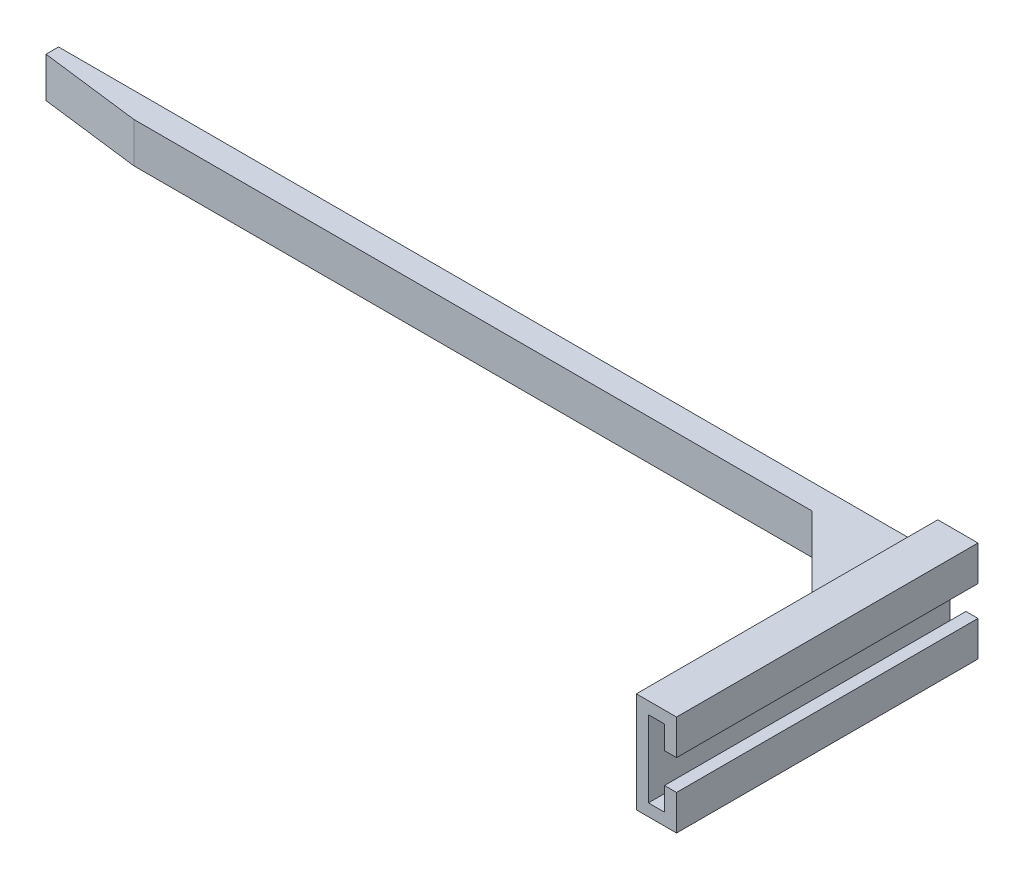
SolidWorks part; units mm, degrees
ref_plane "前视基准面" through (0, 0, 0) normal (0, 0, 1) x (1, 0, 0)
ref_plane "上视基准面" through (0, 0, 0) normal (0, 1, 0) x (1, 0, 0)
ref_plane "右视基准面" through (0, 0, 0) normal (1, 0, 0) x (0, 0, -1)
sketch "草图1" plane through (0, 0, 0) normal (0, 0, 1) x (1, 0, 0)
  line L5 (5.6, 10.6) -> (3.2, 10.6)
  line L6 (0, 0) -> (3.2, 0)
  line L11 (0, 0) -> (0, 15.2)
  line L12 (0, 15.2) -> (3.2, 15.2)
  line L17 (3.2, 0) -> (3.2, 4.6)
  line L18 (-2.4, -2.4) -> (5.6, -2.4)
  line L21 (-2.4, -2.4) -> (-2.4, 17.6)
  line L22 (-2.4, 17.6) -> (5.6, 17.6)
  line L23 (5.6, -2.4) -> (5.6, 4.6)
  line L24 (3.2, 4.6) -> (5.6, 4.6)
  line L25 (3.2, 10.6) -> (3.2, 15.2)
  line L26 (5.6, 10.6) -> (5.6, 17.6)
  point P5 (1.6, 17.6)
  point P9 (1.6, 15.2)
  dimension "D1" = 3.2
  dimension "D2" = 15.2
  dimension "D3" = 8
  dimension "D4" = 20
  dimension "D5" = 0
extrude "凸台-拉伸1" add sketch "草图1" along normal blind 60 contours L12 L25 L5 L26 L22 L21 L18 L23 L24 L17 L6 L11
sketch "草图2" plane through (-2.4, 0, 0) normal (-1, 0, 0) x (0, 0, 1)
  line L0 (0, -2.4) -> (0, 17.6) construction
  line L1 (0, 11.6) -> (5, 11.6)
  line L2 (0, 11.6) -> (0, 3.6)
  line L3 (0, 3.6) -> (5, 3.6)
  line L4 (5, 11.6) -> (5, 3.6)
  line L5 (60, 17.6) -> (0, 17.6) construction
  line L6 (60, -2.4) -> (0, -2.4) construction
  dimension "D1" = 6
  dimension "D2" = 6
  dimension "D3" = 5
extrude "凸台-拉伸2" add sketch "草图2" along normal blind 175 contours L4 L3 L2 L1
chamfer "倒角1" distance 20 angle 45 1 edges at (-2.4, 7.6, 5)
sketch "草图3" plane through (0, 11.6, 0) normal (0, 1, 0) x (1, 0, 0)
  line L0 (-177.4, -2.5) -> (-157.4, -5)
  line L1 (-177.4, 0) -> (-177.4, -5) construction
  line L2 (-177.4, -5) -> (-22.4, -5) construction
  line L3 (-157.4, -5) -> (-177.4, -5)
  line L4 (-177.4, -5) -> (-177.4, -2.5)
  dimension "D1" = 20
extrude "切除-拉伸1" cut sketch "草图3" against normal blind 33.8
chamfer "倒角2" distance 2 angle 45 2 edges at (-2.4, 3.6, 12.5) (-2.4, 11.6, 12.5)
equation "\"60、\"=50"
